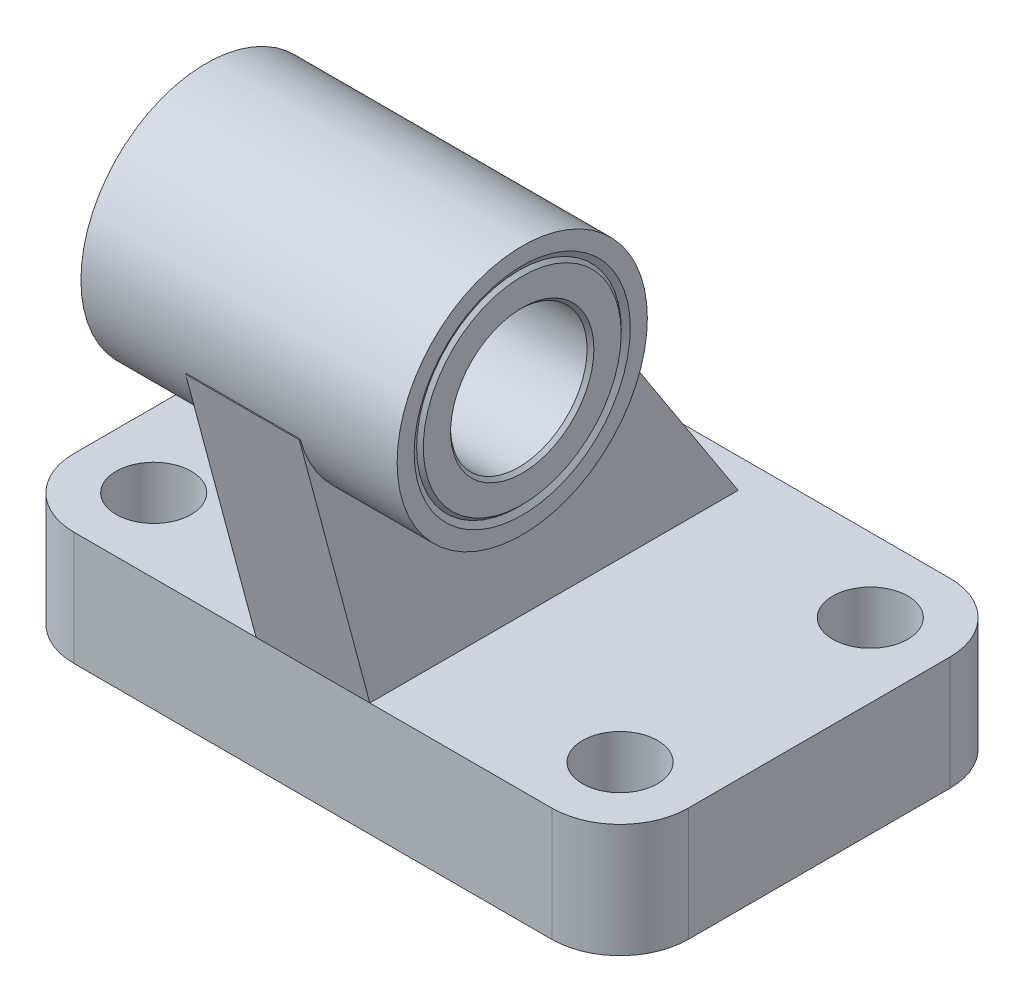
SolidWorks part; units mm, degrees
ref_plane "Front Plane" through (0, 0, 0) normal (0, 0, 1) x (1, 0, 0)
ref_plane "Top Plane" through (0, 0, 0) normal (0, 1, 0) x (1, 0, 0)
ref_plane "Right Plane" through (0, 0, 0) normal (1, 0, 0) x (0, 0, -1)
ref_plane "Plane1" through (0, 0, 0) normal (0, 1, 0) x (1, 0, 0)
sketch "Sketch1" plane through (0, 0, 0) normal (0, 1, 0) x (1, 0, 0)
  line L0 (-21, -17.5) -> (21, -17.5)
  line L1 (27, -11.5) -> (27, 11.5)
  line L2 (21, 17.5) -> (-21, 17.5)
  line L3 (-27, 11.5) -> (-27, -11.5)
  arc A0 (-27, -11.5) -> (-21, -17.5) centre (-21, -11.5) ccw
  arc A1 (21, -17.5) -> (27, -11.5) centre (21, -11.5) ccw
  arc A2 (27, 11.5) -> (21, 17.5) centre (21, 11.5) ccw
  arc A3 (-21, 17.5) -> (-27, 11.5) centre (-21, 11.5) ccw
extrude "Boss-Extrude1" add sketch "Sketch1" along normal blind 10
ref_plane "Plane2" through (0, 0, 0) normal (1, 0, 0) x (0, 0, -1)
sketch "Sketch2" plane through (0, 0, 0) normal (1, 0, 0) x (0, 0, -1)
  line L0 (-23.6986, 33.1333) -> (-17.5, 10)
  line L1 (-17.5, 10) -> (14.8846, 10)
  line L2 (14.8846, 10) -> (-3.6304, 38.5106)
  line L3 (-3.6304, 38.5106) -> (-23.6986, 33.1333)
extrude "Boss-Extrude2" add sketch "Sketch2" against normal blind 5 and the other way blind 5
ref_plane "Plane3" through (0, 0, 0) normal (1, 0, 0) x (0, 0, -1)
sketch "Sketch3" plane through (0, 0, 0) normal (1, 0, 0) x (0, 0, -1)
  circle A0 centre (-13, 36) radius 11
extrude "Boss-Extrude3" add sketch "Sketch3" against normal blind 13.9 and the other way blind 13.9
ref_plane "Plane4" through (0, 0, 11) normal (0, 0, 1) x (1, 0, 0)
sketch "Sketch4" plane through (0, 0, 11) normal (0, 0, 1) x (1, 0, 0)
  line L0 (-20.5, 0) -> (-23.8, 0)
  line L1 (-23.8, 0) -> (-23.8, 10)
  line L2 (-23.8, 10) -> (-20.5, 10)
  line L3 (-20.5, 10) -> (-20.5, 0)
  line L4 (-20.5, 10) -> (-20.5, 0) construction
revolve "Cut-Revolve1" cut sketch "Sketch4" angle 360 about L4
ref_plane "Plane5" through (0, 0, 11) normal (0, 0, 1) x (1, 0, 0)
sketch "Sketch5" plane through (0, 0, 11) normal (0, 0, 1) x (1, 0, 0)
  line L0 (20.5, 0) -> (17.2, 0)
  line L1 (17.2, 0) -> (17.2, 10)
  line L2 (17.2, 10) -> (20.5, 10)
  line L3 (20.5, 10) -> (20.5, 0)
  line L4 (20.5, 10) -> (20.5, 0) construction
revolve "Cut-Revolve2" cut sketch "Sketch5" angle 360 about L4
ref_plane "Plane6" through (0, 0, -11) normal (0, 0, 1) x (1, 0, 0)
sketch "Sketch6" plane through (0, 0, -11) normal (0, 0, 1) x (1, 0, 0)
  line L0 (-20.5, 0) -> (-23.8, 0)
  line L1 (-23.8, 0) -> (-23.8, 10)
  line L2 (-23.8, 10) -> (-20.5, 10)
  line L3 (-20.5, 10) -> (-20.5, 0)
  line L4 (-20.5, 10) -> (-20.5, 0) construction
revolve "Cut-Revolve3" cut sketch "Sketch6" angle 360 about L4
ref_plane "Plane7" through (0, 0, -11) normal (0, 0, 1) x (1, 0, 0)
sketch "Sketch7" plane through (0, 0, -11) normal (0, 0, 1) x (1, 0, 0)
  line L0 (20.5, 0) -> (17.2, 0)
  line L1 (17.2, 0) -> (17.2, 10)
  line L2 (17.2, 10) -> (20.5, 10)
  line L3 (20.5, 10) -> (20.5, 0)
  line L4 (20.5, 10) -> (20.5, 0) construction
revolve "Cut-Revolve4" cut sketch "Sketch7" angle 360 about L4
ref_plane "Plane8" through (0, 0, 13) normal (0, 0, 1) x (1, 0, 0)
sketch "Sketch8" plane through (0, 0, 13) normal (0, 0, 1) x (1, 0, 0)
  line L0 (-13.9, 36) -> (-13.9, 45.5)
  line L1 (-13.9, 45.5) -> (-13.6113, 45)
  line L2 (-13.6113, 45) -> (13.6113, 45)
  line L3 (13.6113, 45) -> (13.9, 45.5)
  line L4 (13.9, 45.5) -> (13.9, 36)
  line L5 (13.9, 36) -> (-13.9, 36)
  line L6 (13.9, 36) -> (-13.9, 36) construction
revolve "Cut-Revolve5" cut sketch "Sketch8" angle 360 about L6
ref_plane "Plane9" through (0, 0, 13) normal (0, 0, 1) x (1, 0, 0)
sketch "Sketch9" plane through (0, 0, 13) normal (0, 0, 1) x (1, 0, 0)
  line L0 (-13.9, 42.3) -> (-13.6, 42)
  line L1 (-13.6, 42) -> (13.6, 42)
  line L2 (13.6, 42) -> (13.9, 42.3)
  line L3 (13.9, 42.3) -> (13.9, 44.7)
  line L4 (13.9, 44.7) -> (13.6, 45)
  line L5 (13.6, 45) -> (-13.6, 45)
  line L6 (-13.6, 45) -> (-13.9, 44.7)
  line L7 (-13.9, 44.7) -> (-13.9, 42.3)
  line L8 (13.9, 36) -> (-13.9, 36) construction
revolve "Revolve1" add sketch "Sketch9" angle 360 about L8
